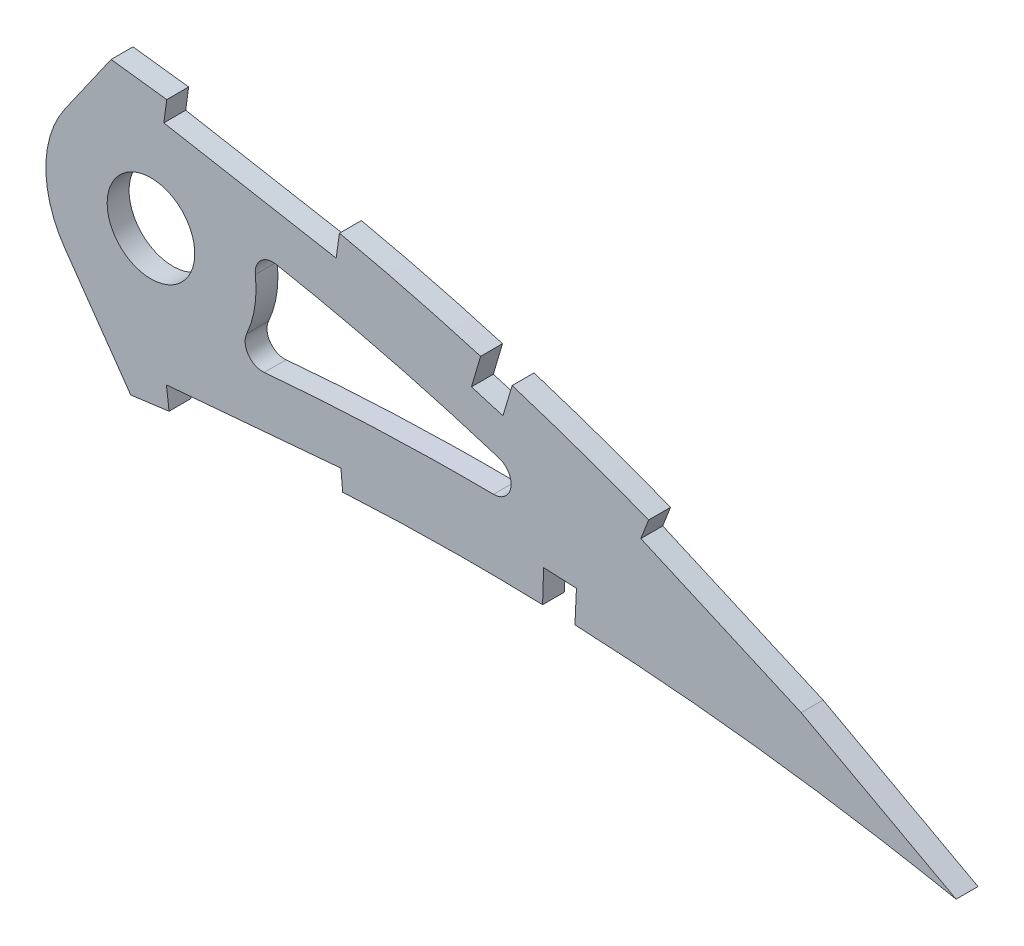
SolidWorks part; units mm, degrees
ref_plane "Front Plane" through (0, 0, 0) normal (0, 0, 1) x (1, 0, 0)
ref_plane "Top Plane" through (0, 0, 0) normal (0, 1, 0) x (1, 0, 0)
ref_plane "Right Plane" through (0, 0, 0) normal (1, 0, 0) x (0, 0, -1)
curve "Curve1"
  spline degree 3 poles (418.0125, 0.6517, 0) (417.9804, 0.6715, 0) (417.8525, 0.7505, 0) (417.5642, 0.9274, 0) (417.084, 1.2219, 0) (416.4119, 1.6322, 0) (415.5483, 2.157, 0) (414.4927, 2.7927, 0) (413.2459, 3.5372, 0) (411.8081, 4.387, 0) (410.1795, 5.3382, 0) (408.3608, 6.3869, 0) (406.352, 7.527, 0) (404.1539, 8.7541, 0) (401.7673, 10.0622, 0) (399.1927, 11.4455, 0) (396.4309, 12.8968, 0) (393.4831, 14.4101, 0) (390.3497, 15.9768, 0) (387.0323, 17.5905, 0) (383.532, 19.2431, 0) (379.8498, 20.9259, 0) (375.9881, 22.6319, 0) (371.9478, 24.3506, 0) (367.7312, 26.0745, 0) (363.3401, 27.7938, 0) (358.7771, 29.5006, 0) (354.0441, 31.184, 0) (349.1444, 32.8365, 0) (344.0806, 34.4474, 0) (338.8562, 36.008, 0) (333.4742, 37.5082, 0) (327.9392, 38.9402, 0) (322.2547, 40.2936, 0) (316.4254, 41.5594, 0) (310.456, 42.7299, 0) (304.3515, 43.7936, 0) (298.1289, 44.7494, 0) (291.8882, 45.5445, 0) (285.6603, 46.3243, 0) (279.4418, 47.0569, 0) (273.1472, 47.7584, 0) (266.7827, 48.425, 0) (260.3545, 49.0544, 0) (253.8692, 49.6441, 0) (247.3335, 50.1923, 0) (240.7538, 50.6959, 0) (234.1369, 51.1541, 0) (227.4895, 51.5628, 0) (220.8185, 51.9218, 0) (214.1308, 52.2286, 0) (207.4334, 52.481, 0) (200.7332, 52.6776, 0) (194.0374, 52.8164, 0) (187.3531, 52.8966, 0) (180.6873, 52.916, 0) (174.0473, 52.8742, 0) (167.44, 52.7698, 0) (160.8726, 52.6014, 0) (154.3521, 52.3686, 0) (147.8856, 52.0716, 0) (141.4801, 51.7078, 0) (135.1426, 51.2797, 0) (128.8802, 50.7853, 0) (122.6997, 50.2246, 0) (116.6076, 49.5999, 0) (110.6107, 48.9095, 0) (104.7154, 48.1553, 0) (98.9282, 47.3389, 0) (93.2555, 46.4598, 0) (87.7035, 45.5205, 0) (82.2781, 44.522, 0) (76.9851, 43.4673, 0) (71.8302, 42.3565, 0) (66.8189, 41.1931, 0) (61.9564, 39.979, 0) (57.2479, 38.7165, 0) (52.6982, 37.4086, 0) (48.3119, 36.0583, 0) (44.0941, 34.667, 0) (40.048, 33.2401, 0) (36.1786, 31.7785, 0) (32.4888, 30.2868, 0) (28.983, 28.767, 0) (25.6637, 27.2237, 0) (22.5348, 25.6586, 0) (19.5984, 24.0762, 0) (16.8576, 22.4789, 0) (14.3149, 20.8697, 0) (11.9714, 19.2526, 0) (9.8303, 17.6287, 0) (7.8925, 16.002, 0) (6.159, 14.375, 0) (4.6325, 12.7489, 0) (3.3127, 11.1265, 0) (2.2016, 9.5091, 0) (1.2991, 7.8983, 0) (0.6075, 6.2951, 0) (0.126, 4.7006, 0) (-0.1376, 3.117, 0) (-0.2032, 1.5431, 0) (-0.0676, 0.5136, 0) (0, 0, 0) knots 0 0 0 0 0.000254 0.001015 0.002283 0.004057 0.006331 0.009105 0.012374 0.016134 0.02038 0.025106 0.030306 0.035972 0.0421 0.048678 0.055702 0.06316 0.071046 0.07935 0.088063 0.097176 0.106678 0.116562 0.126814 0.137428 0.148394 0.1597 0.171338 0.183298 0.19557 0.208144 0.221012 0.234162 0.247587 0.261277 0.275223 0.289414 0.303771 0.317689 0.331784 0.34604 0.360444 0.374983 0.38964 0.404403 0.419257 0.434187 0.449177 0.464215 0.479284 0.49437 0.509458 0.524532 0.539579 0.554583 0.56953 0.584403 0.599191 0.613877 0.628447 0.642889 0.657186 0.671326 0.685294 0.699078 0.712665 0.726043 0.739198 0.752118 0.764792 0.777208 0.789356 0.801224 0.812804 0.824083 0.835055 0.84571 0.856038 0.866034 0.875689 0.884998 0.893953 0.902553 0.910789 0.918661 0.926166 0.933303 0.940071 0.946475 0.952518 0.958205 0.963547 0.968557 0.97325 0.977651 0.981787 0.985694 0.989415 0.993001 0.996508 1 1 1 1
curve "Curve2"
  spline degree 3 poles (0, 0, 0) (0.1073, -0.5067, 0) (0.3225, -1.5225, 0) (0.9071, -2.9849, 0) (1.6803, -4.3906, 0) (2.6581, -5.736, 0) (3.8343, -7.0207, 0) (5.206, -8.246, 0) (6.772, -9.4112, 0) (8.5303, -10.5159, 0) (10.4783, -11.5612, 0) (12.6138, -12.5465, 0) (14.9348, -13.4715, 0) (17.4389, -14.3348, 0) (20.1229, -15.1379, 0) (22.9843, -15.8787, 0) (26.0199, -16.5584, 0) (29.2267, -17.1751, 0) (32.6013, -17.7296, 0) (36.1401, -18.2214, 0) (39.8395, -18.651, 0) (43.6959, -19.0173, 0) (47.7054, -19.3212, 0) (51.8641, -19.5629, 0) (56.168, -19.7432, 0) (60.6128, -19.8613, 0) (65.1943, -19.9191, 0) (69.9083, -19.9175, 0) (74.7502, -19.8561, 0) (79.7159, -19.7382, 0) (84.8006, -19.5631, 0) (89.9997, -19.3329, 0) (95.3085, -19.05, 0) (100.7222, -18.7153, 0) (106.2362, -18.3302, 0) (111.8455, -17.8979, 0) (117.5452, -17.4195, 0) (123.3302, -16.8976, 0) (129.1955, -16.3351, 0) (135.1358, -15.7335, 0) (141.1461, -15.0958, 0) (147.221, -14.4241, 0) (153.3552, -13.7218, 0) (159.5432, -12.9903, 0) (165.7798, -12.2338, 0) (172.059, -11.4536, 0) (178.3757, -10.6529, 0) (184.7241, -9.8353, 0) (191.0984, -9.0009, 0) (197.493, -8.1554, 0) (203.902, -7.2983, 0) (210.3197, -6.4339, 0) (216.7401, -5.5649, 0) (223.157, -4.6917, 0) (229.5648, -3.8177, 0) (235.9575, -2.9455, 0) (242.3289, -2.075, 0) (248.6732, -1.2107, 0) (254.984, -0.3523, 0) (261.2554, 0.4983, 0) (267.4816, 1.3385, 0) (273.6565, 2.1675, 0) (279.7739, 2.9846, 0) (285.8276, 3.7901, 0) (291.7208, 4.5595, 0) (297.4382, 5.334, 0) (302.999, 5.9689, 0) (308.4906, 6.5107, 0) (313.9186, 6.955, 0) (319.2766, 7.3081, 0) (324.5584, 7.5724, 0) (329.7577, 7.7517, 0) (334.868, 7.8514, 0) (339.8828, 7.8739, 0) (344.7953, 7.8264, 0) (349.5992, 7.7127, 0) (354.2877, 7.538, 0) (358.8543, 7.3082, 0) (363.2925, 7.0294, 0) (367.5956, 6.7058, 0) (371.7576, 6.345, 0) (375.7722, 5.9523, 0) (379.6331, 5.5321, 0) (383.3347, 5.0933, 0) (386.8711, 4.6386, 0) (390.237, 4.1757, 0) (393.427, 3.7092, 0) (396.4359, 3.245, 0) (399.2592, 2.7876, 0) (401.8921, 2.3431, 0) (404.3306, 1.9155, 0) (406.5705, 1.5092, 0) (408.6087, 1.1291, 0) (410.4411, 0.7773, 0) (412.0652, 0.4594, 0) (413.4782, 0.1769, 0) (414.6777, -0.0662, 0) (415.6619, -0.269, 0) (416.4292, -0.4281, 0) (416.9781, -0.5438, 0) (417.3079, -0.6126, 0) (417.4545, -0.6439, 0) (417.4911, -0.6517, 0) knots 0 0 0 0 0.003638 0.007293 0.011028 0.014901 0.018963 0.023258 0.027821 0.032679 0.037853 0.043362 0.049215 0.055422 0.061989 0.068918 0.076211 0.083868 0.091887 0.100266 0.109 0.118085 0.127515 0.137285 0.147388 0.157816 0.168563 0.179619 0.190977 0.202627 0.21456 0.226767 0.239236 0.251959 0.264924 0.27812 0.291536 0.30516 0.318981 0.332985 0.347163 0.361499 0.375981 0.390597 0.405333 0.420175 0.43511 0.450124 0.465203 0.480333 0.495501 0.51069 0.525887 0.541078 0.556247 0.571382 0.586466 0.601485 0.616424 0.631269 0.646007 0.660621 0.675098 0.689423 0.703582 0.716908 0.730009 0.742952 0.755726 0.76832 0.780724 0.792927 0.804916 0.816679 0.828204 0.839475 0.850481 0.861208 0.871639 0.881763 0.891564 0.901027 0.910139 0.918884 0.927249 0.935221 0.942785 0.949928 0.956638 0.962904 0.968712 0.974054 0.978918 0.983297 0.98718 0.990561 0.993433 0.995791 0.99763 0.998946 0.999737 1 1 1 1
sketch "Sketch1" plane through (0, 0, 0) normal (0, 0, 1) x (1, 0, 0)
  line L25 (400.7873, -0.6256) -> (404.5887, -1.4136)
  line L26 (401.2878, 0.6256) -> (404.5887, -1.4136)
  spline S4 degree 3 poles (0, 0) (0.103, -0.4865) (0.3096, -1.4616) (0.8709, -2.8654) (1.6131, -4.2149) (2.5518, -5.5065) (3.6808, -6.7398) (4.9977, -7.916) (6.5011, -9.0347) (8.189, -10.0952) (10.0591, -11.0987) (12.1091, -12.0445) (14.3373, -12.9325) (16.7411, -13.7613) (19.3178, -14.5322) (22.0647, -15.2434) (24.9788, -15.8959) (28.0573, -16.488) (31.2969, -17.0202) (34.6941, -17.4924) (38.2455, -17.9047) (41.9476, -18.2564) (45.7967, -18.5482) (49.789, -18.7802) (53.9207, -18.9532) (58.1877, -19.0666) (62.5859, -19.1221) (67.1113, -19.1206) (71.7595, -19.0616) (76.5265, -18.9485) (81.4077, -18.7804) (86.3988, -18.5594) (91.4952, -18.2878) (96.6923, -17.9665) (101.9857, -17.5968) (107.3706, -17.1818) (112.8422, -16.7225) (118.3958, -16.2216) (124.0263, -15.6815) (129.7291, -15.104) (135.4989, -14.4918) (141.3307, -13.847) (147.2195, -13.1728) (153.1599, -12.4706) (159.1469, -11.7443) (165.1749, -10.9954) (171.2389, -10.2267) (177.3333, -9.4418) (183.4525, -8.6407) (189.5913, -7.8291) (195.7439, -7.0063) (201.9048, -6.1765) (208.0683, -5.3423) (214.2285, -4.504) (220.3799, -3.665) (226.5169, -2.8276) (232.6333, -1.992) (238.7238, -1.1622) (244.7821, -0.3382) (250.8026, 0.4783) (256.7796, 1.285) (262.7075, 2.0808) (268.5802, 2.8651) (274.3916, 3.6384) (280.0491, 4.3771) (285.5377, 5.1206) (290.876, 5.73) (296.1479, 6.2502) (301.3588, 6.6767) (306.5024, 7.0157) (311.5728, 7.2694) (316.5641, 7.4416) (321.4699, 7.5373) (326.2841, 7.5589) (331.0001, 7.5133) (335.6118, 7.4042) (340.1127, 7.2364) (344.4965, 7.0158) (348.7571, 6.7481) (352.8881, 6.4375) (356.8836, 6.0912) (360.7375, 5.7142) (364.444, 5.3108) (367.9975, 4.8895) (371.3924, 4.453) (374.6236, 4.0087) (377.686, 3.5608) (380.5745, 3.1152) (383.2848, 2.6761) (385.8124, 2.2493) (388.1534, 1.8389) (390.3037, 1.4488) (392.2603, 1.0839) (394.0193, 0.7462) (395.5785, 0.441) (396.9349, 0.1698) (398.0865, -0.0635) (399.0313, -0.2582) (399.7679, -0.4109) (400.2948, -0.522) (400.6114, -0.5881) (400.7521, -0.6181) (400.7873, -0.6256) knots 0 0 0 0 0.003638 0.007293 0.011028 0.014901 0.018963 0.023258 0.027821 0.032679 0.037853 0.043362 0.049215 0.055422 0.061989 0.068918 0.076211 0.083868 0.091887 0.100266 0.109 0.118085 0.127515 0.137285 0.147388 0.157816 0.168563 0.179619 0.190977 0.202627 0.21456 0.226767 0.239236 0.251959 0.264924 0.27812 0.291536 0.30516 0.318981 0.332985 0.347163 0.361499 0.375981 0.390597 0.405333 0.420175 0.43511 0.450124 0.465203 0.480333 0.495501 0.51069 0.525887 0.541078 0.556247 0.571382 0.586466 0.601485 0.616424 0.631269 0.646007 0.660621 0.675098 0.689423 0.703582 0.716908 0.730009 0.742952 0.755726 0.76832 0.780724 0.792927 0.804916 0.816679 0.828204 0.839475 0.850481 0.861208 0.871639 0.881763 0.891564 0.901027 0.910139 0.918884 0.927249 0.935221 0.942785 0.949928 0.956638 0.962904 0.968712 0.974054 0.978918 0.983297 0.98718 0.990561 0.993433 0.995791 0.99763 0.998946 0.999737 1 1 1 1
  spline S5 degree 3 poles (401.2878, 0.6256) (401.2571, 0.6446) (401.1342, 0.7205) (400.8574, 0.8903) (400.3965, 1.1731) (399.7512, 1.5669) (398.9222, 2.0707) (397.9089, 2.6809) (396.7119, 3.3957) (395.3317, 4.2115) (393.7683, 5.1246) (392.0223, 6.1313) (390.0938, 7.2259) (387.9837, 8.4039) (385.6926, 9.6596) (383.221, 10.9876) (380.5697, 12.3808) (377.7398, 13.8335) (374.7318, 15.3376) (371.5472, 16.8867) (368.1868, 18.4732) (364.652, 20.0887) (360.9448, 21.7264) (357.0661, 23.3763) (353.0182, 25.0312) (348.8028, 26.6817) (344.4225, 28.3203) (339.8788, 29.9363) (335.1752, 31.5227) (330.3139, 33.0692) (325.2985, 34.5673) (320.1319, 36.0075) (314.8184, 37.3822) (309.3612, 38.6814) (303.7652, 39.8966) (298.0346, 41.0203) (292.1744, 42.0414) (286.2007, 42.959) (280.2097, 43.7223) (274.2311, 44.4709) (268.2613, 45.1741) (262.2186, 45.8476) (256.1087, 46.4875) (249.9377, 47.0918) (243.7119, 47.6579) (237.4377, 48.1841) (231.1212, 48.6675) (224.7691, 49.1074) (218.3876, 49.4998) (211.9836, 49.8444) (205.5634, 50.1389) (199.134, 50.3813) (192.7019, 50.57) (186.274, 50.7032) (179.8571, 50.7802) (173.458, 50.7988) (167.0837, 50.7587) (160.7407, 50.6585) (154.4361, 50.4968) (148.1765, 50.2733) (141.9687, 49.9882) (135.8195, 49.639) (129.7355, 49.228) (123.7237, 48.7534) (117.7905, 48.2151) (111.9421, 47.6154) (106.1851, 46.9526) (100.5257, 46.2286) (94.9701, 45.4449) (89.5244, 44.601) (84.1945, 43.6993) (78.9862, 42.7407) (73.9049, 41.7282) (68.9563, 40.6618) (64.1455, 39.5449) (59.4775, 38.3794) (54.9574, 37.1674) (50.5897, 35.9119) (46.3789, 34.6156) (42.3299, 33.28) (38.4457, 31.9102) (34.7311, 30.5071) (31.1889, 29.075) (27.8234, 27.616) (24.6369, 26.1344) (21.6332, 24.632) (18.8143, 23.1129) (16.1831, 21.5796) (13.7421, 20.0347) (11.4924, 18.4823) (9.437, 16.9233) (7.5767, 15.3617) (5.9126, 13.7999) (4.4471, 12.2388) (3.1802, 10.6814) (2.1135, 9.1287) (1.2472, 7.5823) (0.5832, 6.0433) (0.121, 4.5125) (-0.1321, 2.9923) (-0.195, 1.4814) (-0.0649, 0.4931) (0, 0) knots 0 0 0 0 0.000254 0.001015 0.002283 0.004057 0.006331 0.009105 0.012374 0.016134 0.02038 0.025106 0.030306 0.035972 0.0421 0.048678 0.055702 0.06316 0.071046 0.07935 0.088063 0.097176 0.106678 0.116562 0.126814 0.137428 0.148394 0.1597 0.171338 0.183298 0.19557 0.208144 0.221012 0.234162 0.247587 0.261277 0.275223 0.289414 0.303771 0.317689 0.331784 0.34604 0.360444 0.374983 0.38964 0.404403 0.419257 0.434187 0.449177 0.464215 0.479284 0.49437 0.509458 0.524532 0.539579 0.554583 0.56953 0.584403 0.599191 0.613877 0.628447 0.642889 0.657186 0.671326 0.685294 0.699078 0.712665 0.726043 0.739198 0.752118 0.764792 0.777208 0.789356 0.801224 0.812804 0.824083 0.835055 0.84571 0.856038 0.866034 0.875689 0.884998 0.893953 0.902553 0.910789 0.918661 0.926166 0.933303 0.940071 0.946475 0.952518 0.958205 0.963547 0.968557 0.97325 0.977651 0.981787 0.985694 0.989415 0.993001 0.996508 1 1 1 1
extrude "Boss-Extrude1" add sketch "Sketch1" along normal blind 3.175
sketch "Sketch3" plane through (0, 0, 0) normal (0, 0, -1) x (-1, 0, 0)
  circle A1 centre (-279.0745, 26.2554) radius 6.35
extrude "Cut-Extrude2" cut sketch "Sketch3" against normal blind 7.62
sketch "Sketch4" plane through (0, 0, 3.175) normal (0, 0, 1) x (1, 0, 0)
  line L0 (266.5906, 34.9967) -> (273.2984, 44.5763)
  line L1 (266.5906, 17.5141) -> (276.1465, 3.8669)
  line L2 (279.0745, 26.2554) -> (305.0691, 26.2554)
  circle A0 centre (279.0745, 26.2554) radius 6.35 construction
  circle A1 centre (279.0745, 26.2554) radius 6.35
  circle A2 centre (279.0745, 26.2554) radius 15.24
  spline S0 degree 3 poles (-2901.1837, -760.47) (61.5001, 59.5758) (-7.34, 17.6726) (0.8709, -2.8654) (1.6131, -4.2149) (2.5518, -5.5065) (3.6808, -6.7398) (4.9977, -7.916) (6.5011, -9.0347) (8.189, -10.0952) (10.0591, -11.0987) (12.1091, -12.0445) (14.3373, -12.9325) (16.7411, -13.7613) (19.3178, -14.5322) (22.0647, -15.2434) (24.9788, -15.8959) (28.0573, -16.488) (31.2969, -17.0202) (34.6941, -17.4924) (38.2455, -17.9047) (41.9476, -18.2564) (45.7967, -18.5482) (49.789, -18.7802) (53.9207, -18.9532) (58.1877, -19.0666) (62.5859, -19.1221) (67.1113, -19.1206) (71.7595, -19.0616) (76.5265, -18.9485) (81.4077, -18.7804) (86.3988, -18.5594) (91.4952, -18.2878) (96.6923, -17.9665) (101.9857, -17.5968) (107.3706, -17.1818) (112.8422, -16.7225) (118.3958, -16.2216) (124.0263, -15.6815) (129.7291, -15.104) (135.4989, -14.4918) (141.3307, -13.847) (147.2195, -13.1728) (153.1599, -12.4706) (159.1469, -11.7443) (165.1749, -10.9954) (171.2389, -10.2267) (177.3333, -9.4418) (183.4525, -8.6407) (189.5913, -7.8291) (195.7439, -7.0063) (201.9048, -6.1765) (208.0683, -5.3423) (214.2285, -4.504) (220.3799, -3.665) (226.5169, -2.8276) (232.6333, -1.992) (238.7238, -1.1622) (244.7821, -0.3382) (250.8026, 0.4783) (256.7796, 1.285) (262.7075, 2.0808) (268.5802, 2.8651) (274.3916, 3.6384) (280.0491, 4.3771) (285.5377, 5.1206) (290.876, 5.73) (296.1479, 6.2502) (301.3588, 6.6767) (306.5024, 7.0157) (311.5728, 7.2694) (316.5641, 7.4416) (321.4699, 7.5373) (326.2841, 7.5589) (331.0001, 7.5133) (335.6118, 7.4042) (340.1127, 7.2364) (344.4965, 7.0158) (348.7571, 6.7481) (352.8881, 6.4375) (356.8836, 6.0912) (360.7375, 5.7142) (364.444, 5.3108) (367.9975, 4.8895) (371.3924, 4.453) (374.6236, 4.0087) (377.686, 3.5608) (380.5745, 3.1152) (383.2848, 2.6761) (385.8124, 2.2493) (388.1534, 1.8389) (390.3037, 1.4488) (392.2603, 1.0839) (394.0193, 0.7462) (395.5785, 0.441) (396.9349, 0.1698) (398.0865, -0.0635) (399.0313, -0.2582) (399.7679, -0.4109) (400.2948, -0.522) (415.5144, -3.6986) (429.0652, -13.898) (1065.9953, 2924.0142) knots -0.150314 -0.150314 -0.150314 -0.150314 0.003638 0.007293 0.011028 0.014901 0.018963 0.023258 0.027821 0.032679 0.037853 0.043362 0.049215 0.055422 0.061989 0.068918 0.076211 0.083868 0.091887 0.100266 0.109 0.118085 0.127515 0.137285 0.147388 0.157816 0.168563 0.179619 0.190977 0.202627 0.21456 0.226767 0.239236 0.251959 0.264924 0.27812 0.291536 0.30516 0.318981 0.332985 0.347163 0.361499 0.375981 0.390597 0.405333 0.420175 0.43511 0.450124 0.465203 0.480333 0.495501 0.51069 0.525887 0.541078 0.556247 0.571382 0.586466 0.601485 0.616424 0.631269 0.646007 0.660621 0.675098 0.689423 0.703582 0.716908 0.730009 0.742952 0.755726 0.76832 0.780724 0.792927 0.804916 0.816679 0.828204 0.839475 0.850481 0.861208 0.871639 0.881763 0.891564 0.901027 0.910139 0.918884 0.927249 0.935221 0.942785 0.949928 0.956638 0.962904 0.968712 0.974054 0.978918 0.983297 0.98718 0.990561 0.993433 0.995791 0.99763 0.998946 0.999737 1.111561 1.111561 1.111561 1.111561 only from (0, 0) to (400.7873, -0.6256) construction
  spline S1 degree 3 poles (2017.651, 2526.9698) (426.8894, -22.6706) (415.6477, -8.1819) (400.8574, 0.8903) (400.3965, 1.1731) (399.7512, 1.5669) (398.9222, 2.0707) (397.9089, 2.6809) (396.7119, 3.3957) (395.3317, 4.2115) (393.7683, 5.1246) (392.0223, 6.1313) (390.0938, 7.2259) (387.9837, 8.4039) (385.6926, 9.6596) (383.221, 10.9876) (380.5697, 12.3808) (377.7398, 13.8335) (374.7318, 15.3376) (371.5472, 16.8867) (368.1868, 18.4732) (364.652, 20.0887) (360.9448, 21.7264) (357.0661, 23.3763) (353.0182, 25.0312) (348.8028, 26.6817) (344.4225, 28.3203) (339.8788, 29.9363) (335.1752, 31.5227) (330.3139, 33.0692) (325.2985, 34.5673) (320.1319, 36.0075) (314.8184, 37.3822) (309.3612, 38.6814) (303.7652, 39.8966) (298.0346, 41.0203) (292.1744, 42.0414) (286.2007, 42.959) (280.2097, 43.7223) (274.2311, 44.4709) (268.2613, 45.1741) (262.2186, 45.8476) (256.1087, 46.4875) (249.9377, 47.0918) (243.7119, 47.6579) (237.4377, 48.1841) (231.1212, 48.6675) (224.7691, 49.1074) (218.3876, 49.4998) (211.9836, 49.8444) (205.5634, 50.1389) (199.134, 50.3813) (192.7019, 50.57) (186.274, 50.7032) (179.8571, 50.7802) (173.458, 50.7988) (167.0837, 50.7587) (160.7407, 50.6585) (154.4361, 50.4968) (148.1765, 50.2733) (141.9687, 49.9882) (135.8195, 49.639) (129.7355, 49.228) (123.7237, 48.7534) (117.7905, 48.2151) (111.9421, 47.6154) (106.1851, 46.9526) (100.5257, 46.2286) (94.9701, 45.4449) (89.5244, 44.601) (84.1945, 43.6993) (78.9862, 42.7407) (73.9049, 41.7282) (68.9563, 40.6618) (64.1455, 39.5449) (59.4775, 38.3794) (54.9574, 37.1674) (50.5897, 35.9119) (46.3789, 34.6156) (42.3299, 33.28) (38.4457, 31.9102) (34.7311, 30.5071) (31.1889, 29.075) (27.8234, 27.616) (24.6369, 26.1344) (21.6332, 24.632) (18.8143, 23.1129) (16.1831, 21.5796) (13.7421, 20.0347) (11.4924, 18.4823) (9.437, 16.9233) (7.5767, 15.3617) (5.9126, 13.7999) (4.4471, 12.2388) (3.1802, 10.6814) (2.1135, 9.1287) (1.2472, 7.5823) (0.5832, 6.0433) (0.121, 4.5125) (-0.1321, 2.9923) (-1.0517, -19.0697) (77.9711, -35.6336) (-2988.9672, -247.9745) knots -0.119727 -0.119727 -0.119727 -0.119727 0.000254 0.001015 0.002283 0.004057 0.006331 0.009105 0.012374 0.016134 0.02038 0.025106 0.030306 0.035972 0.0421 0.048678 0.055702 0.06316 0.071046 0.07935 0.088063 0.097176 0.106678 0.116562 0.126814 0.137428 0.148394 0.1597 0.171338 0.183298 0.19557 0.208144 0.221012 0.234162 0.247587 0.261277 0.275223 0.289414 0.303771 0.317689 0.331784 0.34604 0.360444 0.374983 0.38964 0.404403 0.419257 0.434187 0.449177 0.464215 0.479284 0.49437 0.509458 0.524532 0.539579 0.554583 0.56953 0.584403 0.599191 0.613877 0.628447 0.642889 0.657186 0.671326 0.685294 0.699078 0.712665 0.726043 0.739198 0.752118 0.764792 0.777208 0.789356 0.801224 0.812804 0.824083 0.835055 0.84571 0.856038 0.866034 0.875689 0.884998 0.893953 0.902553 0.910789 0.918661 0.926166 0.933303 0.940071 0.946475 0.952518 0.958205 0.963547 0.968557 0.97325 0.977651 0.981787 0.985694 0.989415 0.993001 0.996508 1.143972 1.143972 1.143972 1.143972 only from (401.2878, 0.6256) to (0, 0) construction
  spline S2 degree 3 poles (170.9657, -10.2595) (171.053, -10.2484) (173.1729, -9.9776) (177.3333, -9.4418) (183.4525, -8.6407) (189.5913, -7.8291) (195.7439, -7.0063) (201.9048, -6.1765) (208.0683, -5.3423) (214.2285, -4.504) (220.3799, -3.665) (226.5169, -2.8276) (232.6333, -1.992) (238.7238, -1.1622) (244.7821, -0.3382) (250.8026, 0.4783) (256.7796, 1.285) (262.7075, 2.0808) (268.5802, 2.8651) (274.3916, 3.6384) (280.0491, 4.3771) (285.5377, 5.1206) (290.876, 5.73) (296.1479, 6.2502) (301.3588, 6.6767) (306.5024, 7.0157) (311.5728, 7.2694) (316.5641, 7.4416) (321.4699, 7.5373) (326.2841, 7.5589) (331.0001, 7.5133) (335.6118, 7.4042) (340.1127, 7.2364) (344.4965, 7.0158) (348.7571, 6.7481) (352.8881, 6.4375) (356.8836, 6.0912) (360.7375, 5.7142) (364.444, 5.3108) (367.9975, 4.8895) (371.3924, 4.453) (374.6236, 4.0087) (377.686, 3.5608) (380.5745, 3.1152) (383.2848, 2.6761) (385.8124, 2.2493) (388.1534, 1.8389) (390.3037, 1.4488) (392.2603, 1.0839) (394.0193, 0.7462) (395.5785, 0.441) (396.9349, 0.1698) (398.0865, -0.0635) (399.0313, -0.2582) (399.7679, -0.4109) (400.2948, -0.522) (400.6114, -0.5881) (400.7521, -0.6181) (400.7873, -0.6256) knots 0.434464 0.434464 0.434464 0.434464 0.43511 0.450124 0.465203 0.480333 0.495501 0.51069 0.525887 0.541078 0.556247 0.571382 0.586466 0.601485 0.616424 0.631269 0.646007 0.660621 0.675098 0.689423 0.703582 0.716908 0.730009 0.742952 0.755726 0.76832 0.780724 0.792927 0.804916 0.816679 0.828204 0.839475 0.850481 0.861208 0.871639 0.881763 0.891564 0.901027 0.910139 0.918884 0.927249 0.935221 0.942785 0.949928 0.956638 0.962904 0.968712 0.974054 0.978918 0.983297 0.98718 0.990561 0.993433 0.995791 0.99763 0.998946 0.999737 1 1 1 1
  spline S3 degree 3 poles (401.2878, 0.6256) (401.2571, 0.6446) (401.1342, 0.7205) (400.8574, 0.8903) (400.3965, 1.1731) (399.7512, 1.5669) (398.9222, 2.0707) (397.9089, 2.6809) (396.7119, 3.3957) (395.3317, 4.2115) (393.7683, 5.1246) (392.0223, 6.1313) (390.0938, 7.2259) (387.9837, 8.4039) (385.6926, 9.6596) (383.221, 10.9876) (380.5697, 12.3808) (377.7398, 13.8335) (374.7318, 15.3376) (371.5472, 16.8867) (368.1868, 18.4732) (364.652, 20.0887) (360.9448, 21.7264) (357.0661, 23.3763) (353.0182, 25.0312) (348.8028, 26.6817) (344.4225, 28.3203) (339.8788, 29.9363) (335.1752, 31.5227) (330.3139, 33.0692) (325.2985, 34.5673) (320.1319, 36.0075) (314.8184, 37.3822) (309.3612, 38.6814) (303.7652, 39.8966) (298.0346, 41.0203) (292.1744, 42.0414) (286.2007, 42.959) (280.2097, 43.7223) (274.2311, 44.4709) (268.2613, 45.1741) (262.2186, 45.8476) (256.1087, 46.4875) (249.9377, 47.0918) (243.7119, 47.6579) (237.4377, 48.1841) (231.1212, 48.6675) (224.7691, 49.1074) (218.3876, 49.4998) (211.9836, 49.8444) (205.5634, 50.1389) (199.134, 50.3813) (192.7019, 50.57) (186.274, 50.7032) (179.8571, 50.7802) (173.458, 50.7988) (167.0837, 50.7587) (161.2409, 50.6664) (157.5241, 50.5754) (155.922, 50.5301) knots 0 0 0 0 0.000254 0.001015 0.002283 0.004057 0.006331 0.009105 0.012374 0.016134 0.02038 0.025106 0.030306 0.035972 0.0421 0.048678 0.055702 0.06316 0.071046 0.07935 0.088063 0.097176 0.106678 0.116562 0.126814 0.137428 0.148394 0.1597 0.171338 0.183298 0.19557 0.208144 0.221012 0.234162 0.247587 0.261277 0.275223 0.289414 0.303771 0.317689 0.331784 0.34604 0.360444 0.374983 0.38964 0.404403 0.419257 0.434187 0.449177 0.464215 0.479284 0.49437 0.509458 0.524532 0.539579 0.554583 0.56953 0.584403 0.595673 0.595673 0.595673 0.595673
  spline S4 degree 1 poles (395.9481, -8.0181) (156.2094, 40.3741) knots 0 0 1 1 construction
  spline S5 degree 3 poles (395.9481, -8.0181) (395.8164, -7.9367) (395.5582, -7.7783) (394.9955, -7.4332) (394.0424, -6.8518) (392.1237, -5.6929) (388.2547, -3.4045) (380.4507, 1.0238) (364.5268, 9.2971) (345.6713, 17.3312) (326.2751, 23.8103) (311.4847, 27.8675) (299.0245, 30.5508) (288.9197, 32.2938) (282.6871, 33.1714) (277.4493, 33.8279) (272.2457, 34.4775) (263.1549, 35.5432) (250.1285, 36.9071) (234.4874, 38.2654) (213.6108, 39.6964) (187.4885, 40.7356) (166.6354, 40.6691) (156.2094, 40.3741) knots 0 0 0 0 0.001163 0.002327 0.004654 0.009307 0.018615 0.03723 0.074459 0.148918 0.186148 0.223377 0.260607 0.279222 0.297837 0.307144 0.316451 0.335066 0.372296 0.409525 0.446755 0.521214 0.595673 0.595673 0.595673 0.595673
  spline S6 degree 1 poles (169.6788, -0.1814) (402.9068, 9.3108) knots 0 0 1 1 construction
  spline S7 degree 3 poles (169.6788, -0.1814) (179.2247, 1.0375) (198.2901, 3.5703) (222.179, 6.8356) (241.3015, 9.4441) (255.6616, 11.3892) (266.4144, 12.8286) (273.6183, 13.7829) (277.2073, 14.2522) (280.7487, 14.7262) (284.4437, 15.2129) (288.1772, 15.6495) (293.1071, 16.171) (301.7925, 16.9465) (314.2054, 17.6329) (329.1269, 17.7969) (348.9952, 17.1517) (368.7717, 15.2507) (385.8869, 12.5939) (394.4182, 11.0268) (398.6439, 10.1923) (400.6261, 9.7869) (401.5208, 9.6017) (401.9966, 9.5025) (402.416, 9.4142) (402.7476, 9.3448) (402.9068, 9.3108) knots 0.434464 0.434464 0.434464 0.434464 0.505156 0.575848 0.611194 0.64654 0.681886 0.690723 0.699559 0.708396 0.717232 0.726069 0.734905 0.752578 0.787924 0.82327 0.858616 0.929308 0.964654 0.982327 0.991164 0.995582 0.996686 0.997791 0.998895 1 1 1 1
  dimension "D1" = 30.48
  dimension "D2" = 55
  dimension "D3" = 55
extrude "Cut-Extrude6" cut sketch "Sketch4" against normal through all
sketch "Sketch5" plane through (0, 0, 3.175) normal (0, 0, 1) x (1, 0, 0)
  line L0 (306.6201, 9.9169) -> (281.3204, 7.7269)
  line L1 (306.6201, 9.9169) -> (281.3204, 7.7269)
  line L2 (281.3204, 7.7269) -> (281.7013, 4.5749)
  line L3 (281.3204, 7.7269) -> (281.7013, 4.5749)
  line L4 (306.3693, 39.0865) -> (281.3677, 43.5765)
  line L5 (306.3693, 39.0865) -> (281.3677, 43.5765)
  line L6 (281.3677, 43.5765) -> (280.9367, 40.4312)
  line L7 (281.3677, 43.5765) -> (280.9367, 40.4312)
  line L8 (331.4597, 32.7635) -> (326.8931, 34.1544)
  line L9 (331.4597, 32.7635) -> (326.8931, 34.1544)
  line L10 (326.8931, 34.1544) -> (325.5429, 29.5876)
  line L11 (326.8931, 34.1544) -> (325.5429, 29.5876)
  line L12 (340.7668, 11.9079) -> (336.0099, 12.1261)
  line L13 (340.7668, 11.9079) -> (336.0099, 12.1261)
  line L14 (336.0099, 12.1261) -> (335.8576, 7.3665)
  line L15 (336.0099, 12.1261) -> (335.8576, 7.3665)
  line L16 (374.5036, 15.5416) -> (351.258, 25.7734)
  line L17 (374.5036, 15.5416) -> (351.258, 25.7734)
  line L18 (351.258, 25.7734) -> (350.1038, 22.8161)
  line L19 (351.258, 25.7734) -> (350.1038, 22.8161)
  line L20 (397.1881, 3.2602) -> (374.8638, 15.3748)
  line L21 (397.1881, 3.2602) -> (374.8638, 15.3748)
  line L22 (395.6738, 0.4697) -> (397.1881, 3.2602)
  line L23 (395.6738, 0.4697) -> (397.1881, 3.2602)
  line L24 (373.3495, 12.5843) -> (395.6738, 0.4697)
  line L25 (373.3495, 12.5843) -> (395.6738, 0.4697)
  line L26 (350.1038, 22.8161) -> (373.3495, 12.5843)
  line L27 (350.1038, 22.8161) -> (373.3495, 12.5843)
  line L28 (330.1097, 28.2375) -> (331.4597, 32.7635)
  line L29 (330.1097, 28.2375) -> (331.4597, 32.7635)
  line L30 (325.5429, 29.5876) -> (330.1097, 28.2375)
  line L31 (325.5429, 29.5876) -> (330.1097, 28.2375)
  line L32 (340.5502, 7.1838) -> (340.7668, 11.9079)
  line L33 (340.5502, 7.1838) -> (340.7668, 11.9079)
  line L34 (335.8576, 7.3665) -> (340.5502, 7.1838)
  line L35 (335.8576, 7.3665) -> (340.5502, 7.1838)
  line L36 (305.9268, 35.9426) -> (306.3693, 39.0865)
  line L37 (305.9268, 35.9426) -> (306.3693, 39.0865)
  line L38 (280.9367, 40.4312) -> (305.9268, 35.9426)
  line L39 (280.9367, 40.4312) -> (305.9268, 35.9426)
  line L40 (306.8942, 6.7544) -> (306.6201, 9.9169)
  line L41 (306.8942, 6.7544) -> (306.6201, 9.9169)
  line L42 (281.7013, 4.5749) -> (306.8942, 6.7544)
  line L43 (281.7013, 4.5749) -> (306.8942, 6.7544)
  line L44 (281.3677, 43.5765) -> (281.9443, 46.7871)
  line L45 (306.3693, 39.0865) -> (306.8451, 41.736)
  line L46 (351.258, 25.7734) -> (353.1715, 30.1208)
  line L47 (353.1715, 30.1208) -> (440.7738, 23.0137)
  line L48 (440.7738, 23.0137) -> (440.7738, -24.0045)
  line L49 (440.7738, -24.0045) -> (395.6738, 0.4697)
  line L50 (335.8576, 7.3665) -> (335.8167, 6.0873)
  line L51 (340.5502, 7.1838) -> (340.4626, 5.2737)
extrude "Cut-Extrude8" cut sketch "Sketch5" against normal through all
fillet "Fillet1" radius 2.54 3 edges at (345.2808, 17.1385, 1.5875) (293.3783, 31.5147, 1.5875) (290.2225, 15.8641, 1.5875)
